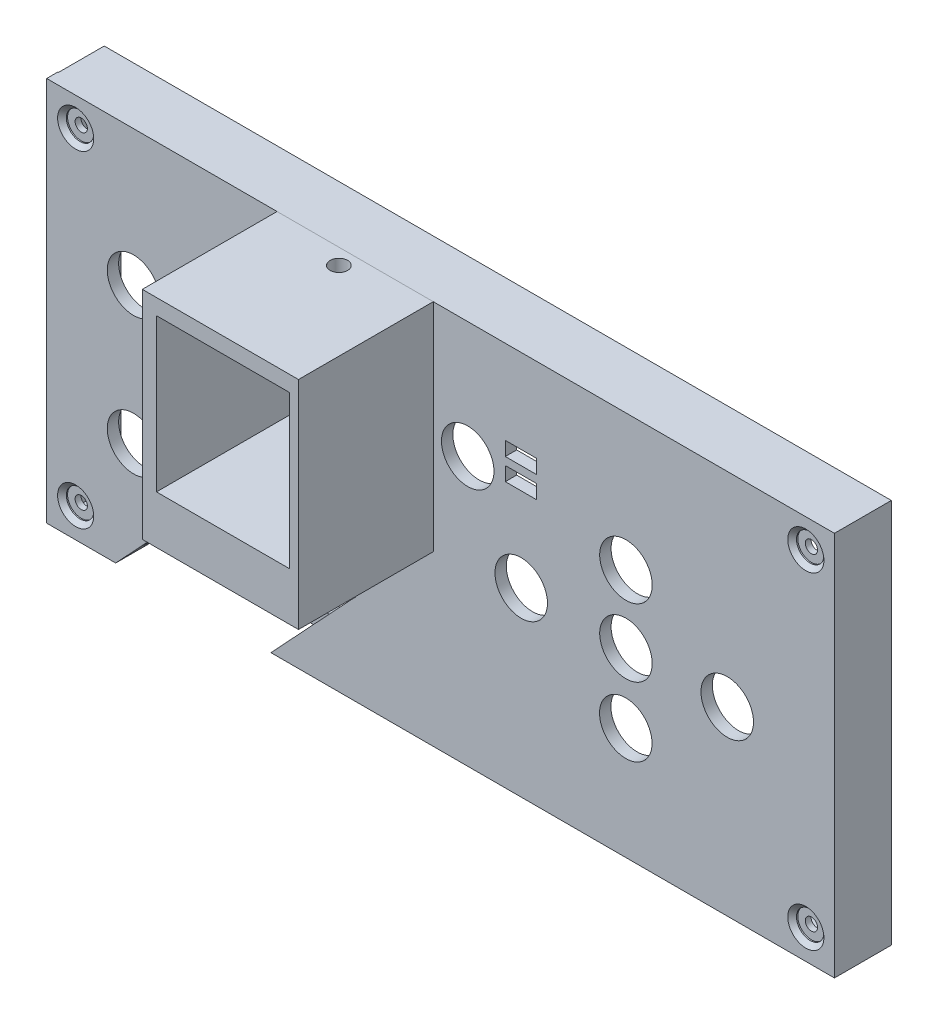
SolidWorks part; units mm, degrees
ref_plane "Front Plane" through (0, 0, 0) normal (0, 0, 1) x (1, 0, 0)
ref_plane "Top Plane" through (0, 0, 0) normal (0, 1, 0) x (1, 0, 0)
ref_plane "Right Plane" through (0, 0, 0) normal (1, 0, 0) x (0, 0, -1)
sketch "Sketch1" plane through (0, 0, 0) normal (0, 0, 1) x (1, 0, 0)
  line L0 (2994.9516, 13542.1893) -> (2994.9516, 13497.3837) construction
  line L1 (2937.8016, 13545.1865) -> (3052.1016, 13545.1865) construction
  line L2 (2943.1972, 13550.2491) -> (3057.4972, 13550.2491)
  line L3 (2943.1972, 13550.2491) -> (2943.1972, 13494.3691)
  line L4 (2943.1972, 13494.3691) -> (3057.4972, 13494.3691)
  line L5 (3057.4972, 13550.2491) -> (3057.4972, 13494.3691)
  line L6 (2943.1972, 13550.2491) -> (3057.4972, 13494.3691) construction
  line L7 (2943.1972, 13494.3691) -> (3057.4972, 13550.2491) construction
  line L8 (3052.1016, 13494.3865) -> (3052.1016, 13545.1865) construction
  point P2 (2994.9516, 13519.7865)
  dimension "D1" = 114.3
  dimension "D2" = 55.88
extrude "Boss-Extrude1" add sketch "Sketch1" along normal blind 1.651
sketch "Sketch2" plane through (0, 0, 0) normal (0, 0, 1) x (1, 0, 0)
  line L0 (3009.7412, 13534.8887) -> (3014.2624, 13534.8887)
  line L1 (3009.7412, 13538.0505) -> (3014.2624, 13538.0505)
  line L2 (3009.7412, 13538.0505) -> (3009.7412, 13536.0185)
  line L3 (3009.7412, 13536.0185) -> (3014.2624, 13536.0185)
  line L4 (3014.2624, 13538.0505) -> (3014.2624, 13536.0185)
  line L5 (3009.7412, 13538.0505) -> (3014.2624, 13536.0185) construction
  line L6 (3009.7412, 13536.0185) -> (3014.2624, 13538.0505) construction
  line L7 (3009.7412, 13534.8887) -> (3009.7412, 13532.8567)
  line L8 (3009.7412, 13532.8567) -> (3014.2624, 13532.8567)
  line L9 (3014.2624, 13534.8887) -> (3014.2624, 13532.8567)
  line L10 (3009.7412, 13534.8887) -> (3014.2624, 13532.8567) construction
  line L11 (3009.7412, 13532.8567) -> (3014.2624, 13534.8887) construction
  line L12 (2997.9588, 13534.8887) -> (2997.9588, 13525.8238)
  line L13 (2975.7331, 13518.4896) -> (2953.2133, 13494.3691)
  line L14 (2975.7331, 13518.4896) -> (2976.3526, 13519.1092)
  line L15 (2975.7331, 13494.3691) -> (2987.3794, 13506.8433)
  line L16 (2975.7331, 13494.3691) -> (2953.2133, 13494.3691)
  line L17 (2943.1972, 13494.3691) -> (3057.4972, 13494.3691) construction
  line L18 (2976.3526, 13519.1092) -> (2987.999, 13507.4629)
  line L19 (2987.999, 13507.4629) -> (2987.3794, 13506.8433)
  line L20 (2997.9588, 13525.8238) -> (2978.6873, 13525.8238)
  line L21 (2978.6873, 13525.8238) -> (2978.6873, 13547.8045)
  line L23 (2978.6873, 13547.8045) -> (2997.9588, 13547.8045)
  line L24 (2997.9588, 13547.8045) -> (2997.9588, 13534.8887)
  circle A0 centre (3027.2483, 13530.5077) radius 3.81
  circle A1 centre (3012.0505, 13520.653) radius 3.81
  circle A2 centre (3027.2483, 13520.653) radius 3.81
  circle A3 centre (3041.941, 13520.653) radius 3.81
  circle A4 centre (3027.2225, 13510.6227) radius 3.81
  circle A5 centre (3004.2884, 13533.3306) radius 3.81
  circle A6 centre (2955.7997, 13530.5831) radius 3.81
  circle A7 centre (2955.7997, 13510.6733) radius 3.81
  point P16 (3012.0018, 13537.0345)
  point P21 (3012.0018, 13533.8727)
  dimension "D1" = 7.62
  dimension "D2" = 7.62
  dimension "D3" = 7.62
  dimension "D4" = 7.62
  dimension "D5" = 7.62
  dimension "D6" = 7.62
  dimension "D7" = 7.62
  dimension "D8" = 7.62
  dimension "D9" = 4.5212
  dimension "D10" = 2.032
  dimension "D11" = 2
extrude "Cut-Extrude2" cut sketch "Sketch2" along normal through all
sketch "Sketch3" plane through (0, 0, 1.651) normal (0, 0, 1) x (1, 0, 0)
  line L0 (2999.292, 13550.2491) -> (2999.292, 13518.8318)
  line L1 (3057.4972, 13550.2491) -> (2943.1972, 13550.2491) construction
  line L2 (2999.292, 13518.8318) -> (2976.63, 13518.8318)
  line L3 (2987.999, 13507.4629) -> (2976.3526, 13519.1092) construction
  line L4 (2976.63, 13518.8318) -> (2976.63, 13550.2491)
  line L5 (3057.4972, 13550.2491) -> (2943.1972, 13550.2491) construction
  line L6 (2976.63, 13550.2491) -> (2999.292, 13550.2491)
extrude "Boss-Extrude2" add sketch "Sketch3" along normal blind 19.558 separate body
sketch "Sketch7" plane through (0, 0, 1.651) normal (0, 0, -1) x (-1, 0, 0)
  line L1 (-2997.9588, 13547.9678) -> (-2978.6873, 13547.9678)
  line L2 (-2997.9588, 13547.9678) -> (-2997.9588, 13525.8238)
  line L3 (-2997.9588, 13525.8238) -> (-2978.6873, 13525.8238)
  line L4 (-2978.6873, 13547.9678) -> (-2978.6873, 13525.8238)
extrude "Cut-Extrude5" cut sketch "Sketch7" against normal through all
sketch "Sketch8" plane through (0, 0, 0) normal (0, 0, -1) x (-1, 0, 0)
  line L0 (-3057.4972, 13494.3691) -> (-3057.4972, 13550.2491) construction
  line L1 (-3057.4972, 13550.2491) -> (-2943.2926, 13550.2491)
  line L2 (-3057.4972, 13550.2491) -> (-3057.4972, 13494.3691)
  line L3 (-3057.4972, 13494.3691) -> (-2943.2926, 13494.3691)
  line L4 (-2943.2926, 13550.2491) -> (-2943.2926, 13494.3691)
  line L5 (-2997.9588, 13547.8045) -> (-3055.0526, 13547.8045) construction
  line L6 (-2997.9588, 13547.8045) -> (-2978.6873, 13547.8045) construction
  line L7 (-2977.4265, 13546.8474) -> (-2945.7372, 13546.8474) construction
  line L8 (-2945.7372, 13546.8474) -> (-2945.7372, 13496.8137) construction
  line L10 (-3055.0526, 13547.8045) -> (-2945.7372, 13547.8045)
  line L11 (-3055.0526, 13547.8045) -> (-3055.0526, 13496.8137)
  line L12 (-3055.0526, 13496.8137) -> (-2945.7372, 13496.8137)
  line L13 (-2945.7372, 13547.8045) -> (-2945.7372, 13496.8137)
  dimension "D1" = 2.4446
  dimension "D2" = 2.4446
  dimension "D3" = 2.4446
  dimension "D4" = 2.4446
extrude "Boss-Extrude4" add sketch "Sketch8" along normal blind 6.604
sketch "Sketch9" plane through (0, 13550.2491, 0) normal (0, 1, 0) x (1, 0, 0)
  circle A0 centre (2987.8852, -3.9395) radius 1.27
  dimension "D1" = 2.54
extrude "Cut-Extrude6" cut sketch "Sketch9" against normal blind 2.032
sketch "Sketch10" plane through (0, 13494.3691, 0) normal (0, -1, 0) x (1, 0, 0)
  line L1 (2953.2133, 0) -> (2975.7331, 0)
  line L2 (2953.2133, 0) -> (2953.2133, -4.9672)
  line L3 (2953.2133, -4.9672) -> (2975.7331, -4.9672)
  line L4 (2975.7331, 0) -> (2975.7331, -4.9672)
extrude "Cut-Extrude7" cut sketch "Sketch10" along direction (0.6824, 0.7309, 0) on the side against the normal blind 12.7
hole_wizard "CBORE for #0 Binding Head Machine Screw1" positions "Sketch13" profile "Sketch12" counterbore size "#0" standard "ANSI Inch" end condition through all
sketch "Sketch13" plane through (0, 0, 1.651) normal (0, 0, 1) x (1, 0, 0)
  point P0 (3053.3464, 13546.0905)
  point P3 (3053.3464, 13498.6651)
  point P5 (2947.4033, 13546.0905)
  point P7 (2947.4033, 13498.6651)
sketch "Sketch12" plane through (3053.3464, 13546.0905, 1.651) normal (1, 0, 0) x (0, -1, 0)
  line L0 (0, 0) -> (0, 8.255)
  line L1 (0, 8.255) -> (0.889, 8.255)
  line L3 (0.889, 8.255) -> (0.889, 0.8128)
  line L4 (1.985, 0.8128) -> (0.889, 0.8128)
  line L5 (1.985, 0.8128) -> (1.985, 0.635)
  line L6 (1.985, 0.635) -> (2.62, 0)
  line L7 (2.62, 0) -> (0, 0)
  line L8 (-1.985, 0.635) -> (-2.62, 0) construction
  line L11 (0, -6.35) -> (0, 107.95) construction
  dimension "Thru Hole Dia." = 1.778
  dimension "Thru Hole Depth" = 8.255
  dimension "C'Bore Dia." = 3.97
  dimension "C'Bore Depth" = 0.8128
  dimension "Near C'Sink Dia." = 5.24
  dimension "Near C'Sink Angle" = 90
equation "\"hole\"=0.3"
equation "\"button_hole\"=0.3"
equation "\"D1@Sketch2\"=\"button_hole\""
equation "\"D2@Sketch2\"=\"button_hole\""
equation "\"D3@Sketch2\"=\"button_hole\""
equation "\"D4@Sketch2\"=\"button_hole\""
equation "\"D5@Sketch2\"=\"button_hole\""
equation "\"D6@Sketch2\"=\"button_hole\""
equation "\"D7@Sketch2\"=\"button_hole\""
equation "\"D8@Sketch2\"=\"button_hole\""
equation "\"led_hole_length\"=0.178"
equation "\"D9@Sketch2\"=\"led_hole_length\""
equation "\"led_hole_height\"=0.08"
equation "\"D10@Sketch2\"=\"led_hole_height\""
equation "\"D2@Sketch8\"=\"D1@Sketch8\""
equation "\"D3@Sketch8\"=\"D1@Sketch8\""
equation "\"D4@Sketch8\"=\"D3@Sketch8\""
